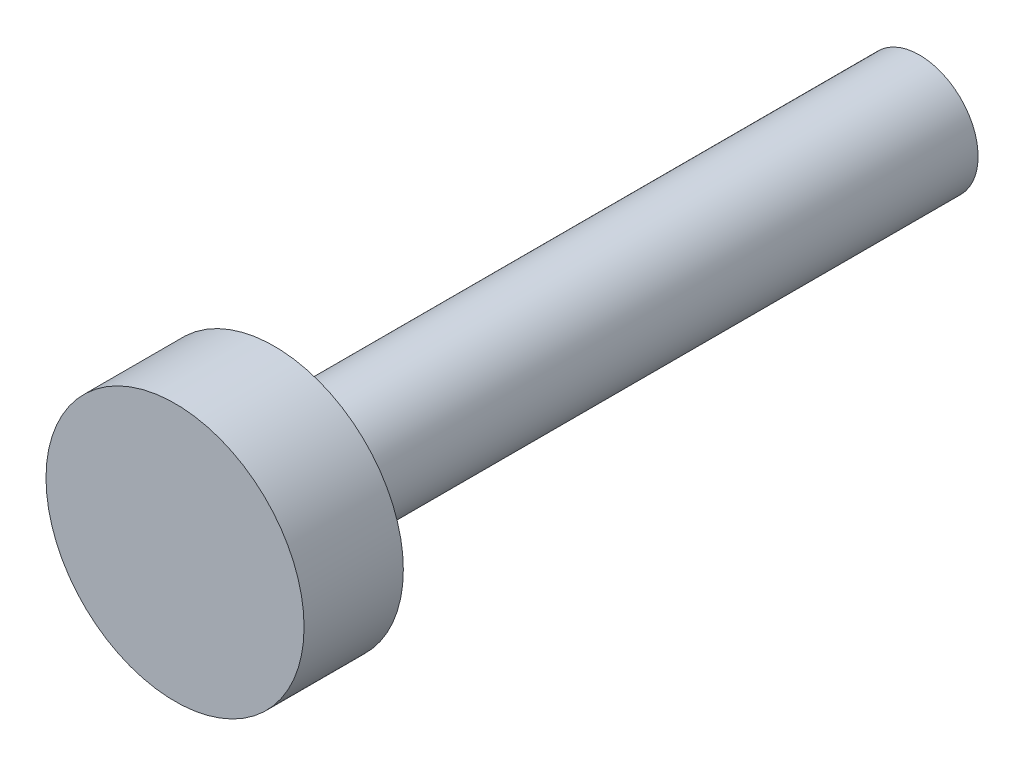
SolidWorks part; units mm, degrees
ref_plane "Front Plane" through (0, 0, 0) normal (0, 0, 1) x (1, 0, 0)
ref_plane "Top Plane" through (0, 0, 0) normal (0, 1, 0) x (1, 0, 0)
ref_plane "Right Plane" through (0, 0, 0) normal (1, 0, 0) x (0, 0, -1)
sketch "Sketch1" plane through (0, 0, 0) normal (0, 0, 1) x (1, 0, 0)
  circle A0 centre (0, 0) radius 3.302
extrude "Extrude1" add sketch "Sketch1" along normal blind 19.05
sketch "Sketch2" plane through (0, 0, 0) normal (0, 0, -1) x (-1, 0, 0)
  circle A0 centre (0, 0) radius 1.5
extrude "Extrude2" cut sketch "Sketch2" against normal blind 16.51 flip side to cut
